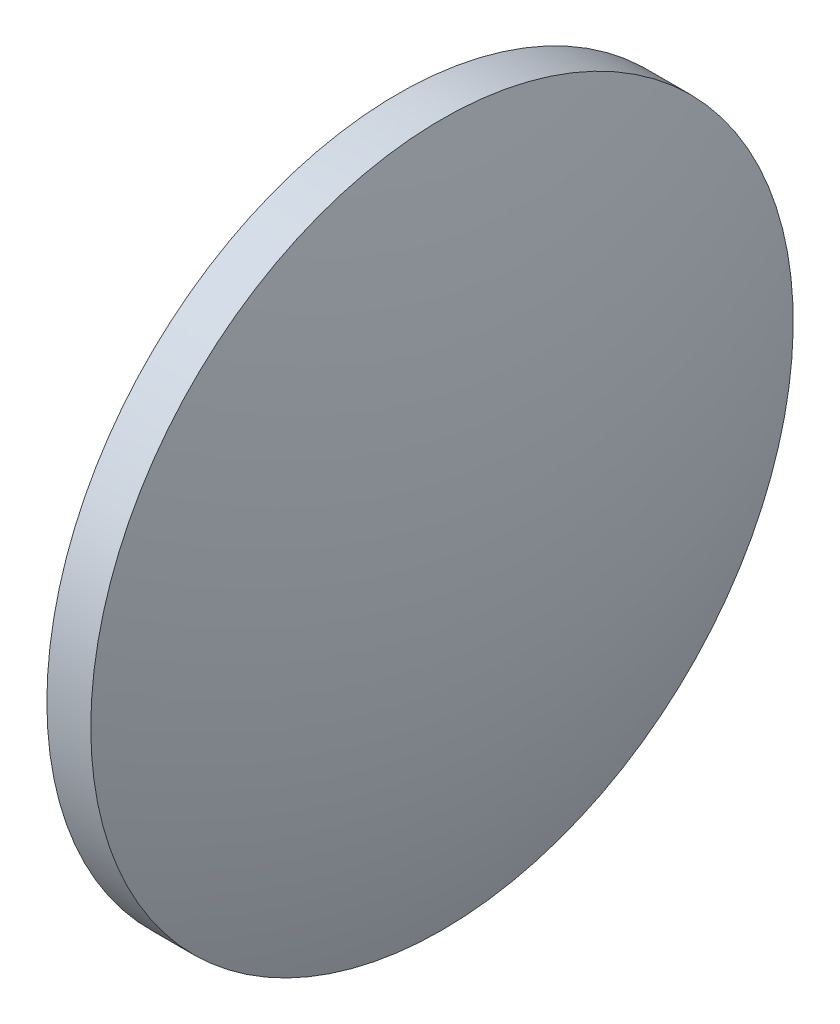
SolidWorks part; units mm, degrees
ref_plane "前视基准面" through (0, 0, 0) normal (0, 0, 1) x (1, 0, 0)
ref_plane "上视基准面" through (0, 0, 0) normal (0, 1, 0) x (1, 0, 0)
ref_plane "右视基准面" through (0, 0, 0) normal (1, 0, 0) x (0, 0, -1)
sketch "草图1" plane through (0, 0, 0) normal (0, 0, 1) x (1, 0, 0)
  line L0 (621.9287, 80.1895) -> (641.1048, 80.1895) construction
  line L1 (626.6232, 80.1895) -> (626.6232, 100.1895)
  line L2 (632.3032, 80.1895) -> (626.6232, 80.1895)
  line L5 (629.1232, 100.1895) -> (626.6232, 100.1895)
  arc A0 (632.3032, 80.1895) -> (629.1232, 100.1895) centre (567.8201, 80.1895) ccw
revolve "旋转1" add sketch "草图1" angle 360 about L0
